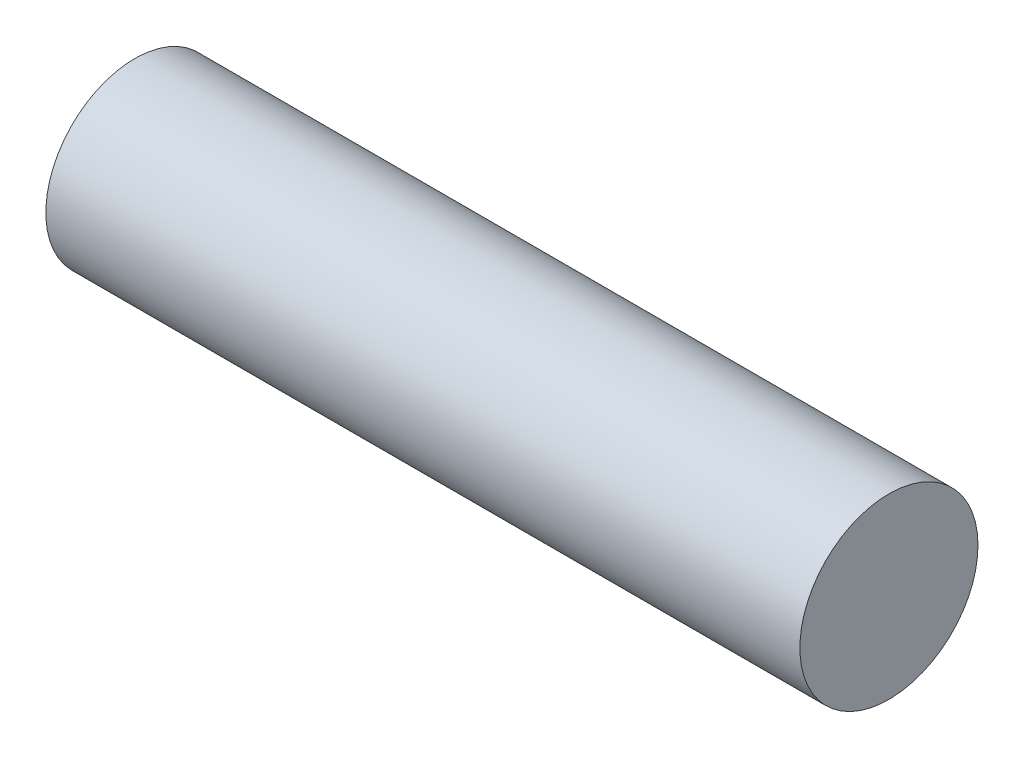
SolidWorks part; units mm, degrees
ref_plane "Front Plane" through (0, 0, 0) normal (0, 0, 1) x (1, 0, 0)
ref_plane "Top Plane" through (0, 0, 0) normal (0, 1, 0) x (1, 0, 0)
ref_plane "Right Plane" through (0, 0, 0) normal (1, 0, 0) x (0, 0, -1)
sketch "Sketch1" plane through (0, 0, 0) normal (1, 0, 0) x (0, 0, -1)
  circle A0 centre (0, 0) radius 6
  dimension "D1" = 12
extrude "Boss-Extrude1" add sketch "Sketch1" against normal blind 50.8
